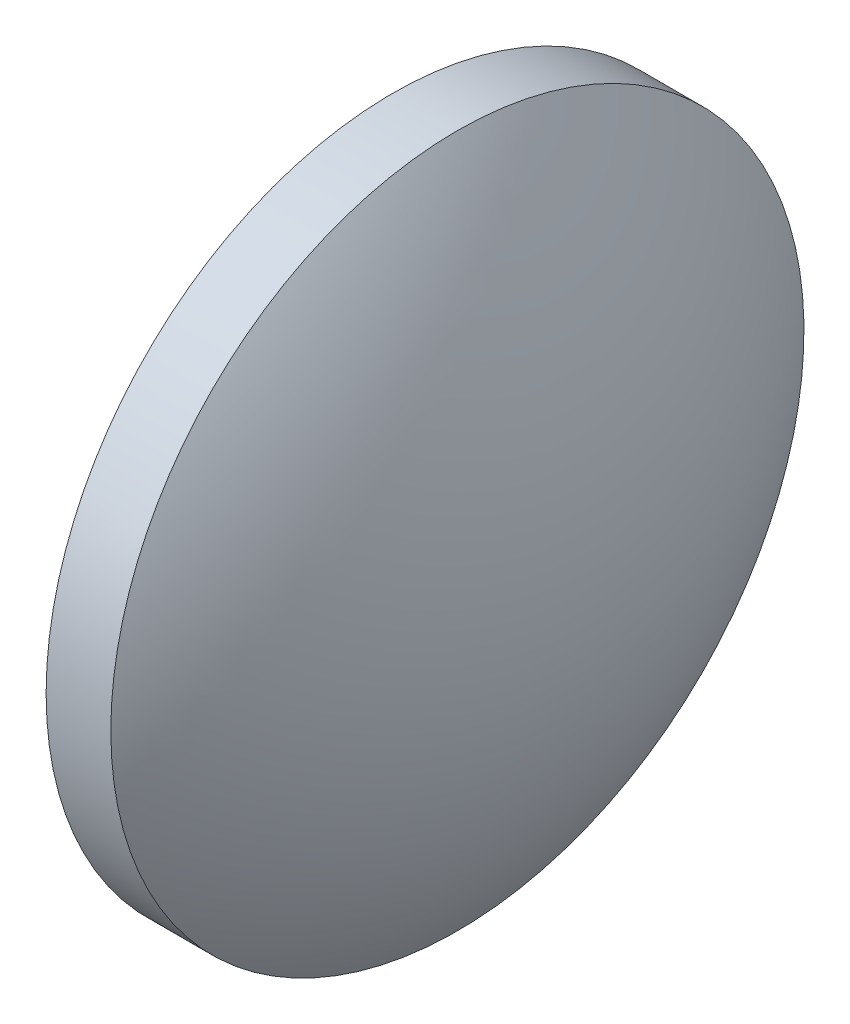
SolidWorks part; units mm, degrees
ref_plane "前视基准面" through (0, 0, 0) normal (0, 0, 1) x (1, 0, 0)
ref_plane "上视基准面" through (0, 0, 0) normal (0, 1, 0) x (1, 0, 0)
ref_plane "右视基准面" through (0, 0, 0) normal (1, 0, 0) x (0, 0, -1)
sketch "草图1" plane through (0, 0, 0) normal (0, 0, 1) x (1, 0, 0)
  line L0 (327.3857, 134.7012) -> (381.1687, 134.7012) construction
  line L1 (345.8591, 134.7012) -> (345.8591, 140.7012)
  line L2 (345.8591, 140.7012) -> (346.9791, 140.7012)
  line L3 (348.8591, 134.7012) -> (345.8591, 134.7012)
  arc A0 (348.8591, 134.7012) -> (346.9791, 140.7012) centre (338.3446, 134.7012) ccw
revolve "旋转1" add sketch "草图1" angle 360 about L0
